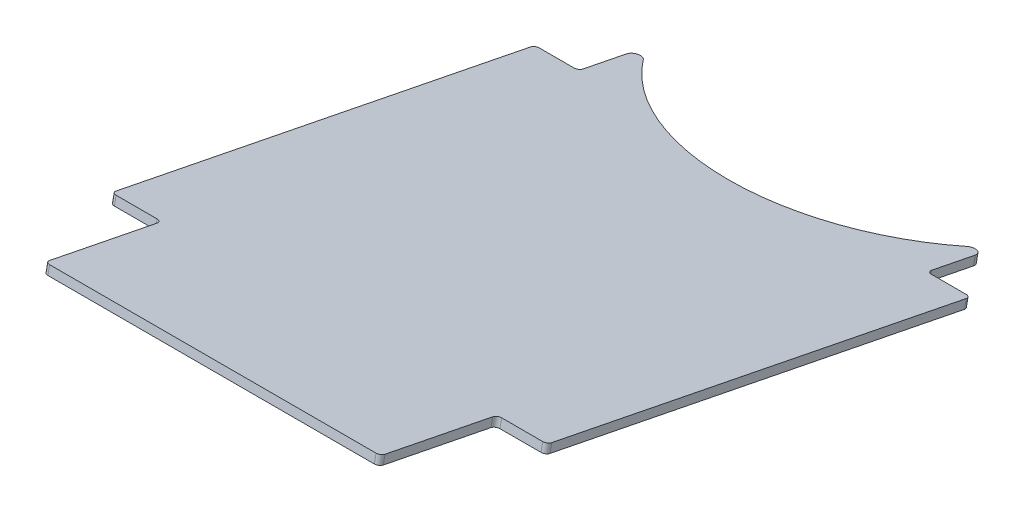
SolidWorks part; units mm, degrees
material "PC High Viscosity"
ref_plane "Front Plane" through (0, 0, 0) normal (0, 0, 1) x (1, 0, 0)
ref_plane "Top Plane" through (0, 0, 0) normal (0, 1, 0) x (1, 0, 0)
ref_plane "Right Plane" through (0, 0, 0) normal (1, 0, 0) x (0, 0, -1)
sketch "Sketch1" plane through (0, 0, 0) normal (1, 0, 0) x (0, 0, -1)
  line L0 (0, 0) -> (0, 38.1) construction
  line L1 (0, 38.1) -> (-1.2388, 31.872)
  line L2 (0, 38.1) -> (-425.45, 122.7273)
  line L3 (-1.2388, 31.872) -> (-426.6888, 116.4993)
  line L4 (-425.45, 122.7273) -> (-426.6888, 116.4993)
  line L6 (0, 0) -> (-44.45, 0) construction
  line L7 (0, 0) -> (0, 431.8) construction
  line L8 (0, 431.8) -> (-44.45, 431.8) construction
  line L9 (-44.45, 0) -> (-44.45, 431.8) construction
  line L10 (-381, 0) -> (-425.45, 0) construction
  line L11 (-381, 0) -> (-381, 431.8) construction
  line L12 (-381, 431.8) -> (-425.45, 431.8) construction
  line L13 (-425.45, 0) -> (-425.45, 431.8) construction
  dimension "D1" = 38.1
  dimension "D2" = 6.35
  dimension "D3" = 11.25
  dimension "D4" = 431.8
  dimension "D5" = 44.45
  dimension "D6" = 0
  dimension "D7" = 381
extrude "Boss-Extrude1" add sketch "Sketch1" along normal blind 317.5
sketch "Sketch2" plane through (0, 36.6499, -7.2901) normal (0, 0.9808, -0.1951) x (1, 0, 0)
  line L0 (0, -7.4329) -> (31.75, -7.4329)
  line L1 (0, -7.4329) -> (0, -441.218) construction
  line L2 (292.1, -224.3255) -> (25.4, -224.3255) construction
  line L8 (0, 0) -> (0, -84.24) construction
  line L9 (31.75, -7.4329) -> (31.75, -78.1538)
  line L10 (31.75, -78.1538) -> (0, -78.1538)
  line L11 (0, -7.4329) -> (0, -441.218) construction
  line L12 (0, -392.7222) -> (36.5125, -392.7222)
  line L13 (0, -373.6792) -> (0, -457.9192) construction
  line L14 (36.5125, -392.7222) -> (36.5125, -441.218)
  line L15 (317.5, -441.218) -> (0, -441.218) construction
  line L16 (36.5125, -441.218) -> (0, -441.218)
  line L17 (0, -441.218) -> (0, -392.7222)
  line L18 (0, -7.4329) -> (0, -78.1538)
  line L19 (158.75, -7.4329) -> (158.75, -441.218) construction
  line L20 (317.5, -7.4329) -> (0, -7.4329) construction
  line L21 (317.5, -7.4329) -> (317.5, -78.1538)
  line L22 (317.5, -441.218) -> (317.5, -392.7222)
  line L23 (280.9875, -441.218) -> (317.5, -441.218)
  line L24 (280.9875, -392.7222) -> (280.9875, -441.218)
  line L25 (317.5, -392.7222) -> (280.9875, -392.7222)
  line L26 (285.75, -78.1538) -> (317.5, -78.1538)
  line L27 (285.75, -7.4329) -> (285.75, -78.1538)
  line L28 (317.5, -7.4329) -> (285.75, -7.4329)
  point P2 (0, -52.7538)
  point P3 (0, -7.4329)
  point P11 (0, -395.8972)
  point P29 (317.5, -395.8972)
  point P30 (317.5, -7.4329)
  point P31 (317.5, -52.7538)
  point P42 (158.75, -224.3255)
  dimension "D1" = 25.4
  dimension "D2" = 266.7
  dimension "D3" = 31.75
  dimension "D4" = 3.175
  dimension "D5" = 6.35
  dimension "D6" = 4.7625
extrude "Cut-Extrude1" cut sketch "Sketch2" against normal through all
sketch "Sketch5" plane through (0, 30.4219, -6.0513) normal (0, -0.9808, 0.1951) x (1, 0, 0)
  line L1 (36.5125, 441.218) -> (280.9875, 441.218)
  line L2 (36.5125, 441.218) -> (36.5125, 479.318)
  line L3 (36.5125, 479.318) -> (280.9875, 479.318)
  line L4 (280.9875, 441.218) -> (280.9875, 479.318)
  dimension "D1" = 38.1
extrude "Boss-Extrude2" add sketch "Sketch5" against normal up to surface (6.35 mm away) up to face at (158.75, 81.8589, 219.991)
sketch "Sketch6" plane through (0, 30.4219, -6.0513) normal (0, -0.9808, 0.1951) x (1, 0, 0)
  line L0 (285.75, 7.4329) -> (31.75, 7.4329) construction
  line L1 (285.75, 7.4329) -> (285.75, 78.1538) construction
  line L2 (31.75, 78.1538) -> (31.75, 7.4329) construction
  line L3 (31.75, 26.4829) -> (31.75, 7.4329)
  line L4 (31.75, 7.4329) -> (285.75, 7.4329)
  line L5 (285.75, 7.4329) -> (285.75, 26.4829)
  arc A0 (31.75, 26.4829) -> (285.75, 26.4829) centre (158.75, -54.0466) cw
  point P5 (158.75, 7.4329)
  dimension "D1" = 88.9
  dimension "D2" = 19.05
extrude "Cut-Extrude3" cut sketch "Sketch6" against normal through all
fillet "Fillet3" radius 5.08 2 edges at (285.75, 38.7025, 19.3034) (31.75, 38.7025, 19.3034)
fillet "Fillet4" radius 3.302 10 edges at (36.5125, 110.1522, 378.5054) (280.9875, 110.1522, 378.5054) (285.75, 48.783, 69.9814) (31.75, 48.783, 69.9814) (0, 48.783, 69.9814) (0, 110.1522, 378.5054) (36.5125, 127.0462, 463.4373) (280.9875, 127.0462, 463.4373) (317.5, 110.1522, 378.5054) (317.5, 48.783, 69.9814)
